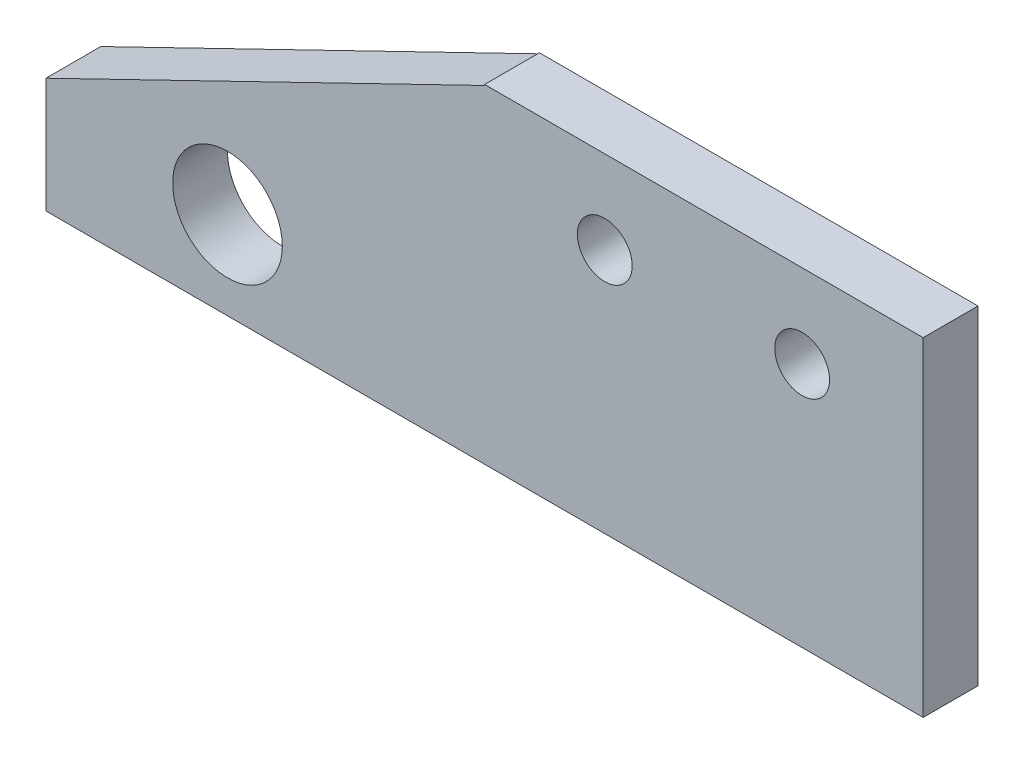
SolidWorks part; units mm, degrees
material "1060 Alloy"
ref_plane "Front Plane" through (0, 0, 0) normal (0, 0, 1) x (1, 0, 0)
ref_plane "Top Plane" through (0, 0, 0) normal (0, 1, 0) x (1, 0, 0)
ref_plane "Right Plane" through (0, 0, 0) normal (1, 0, 0) x (0, 0, -1)
sketch "Sketch4" plane through (0, 0, 0) normal (0, 0, 1) x (1, 0, 0)
  line L0 (-12.7, 4.699) -> (-5.7404, 4.699) construction
  line L1 (-12.7, 9.525) -> (12.7, 9.525)
  line L2 (-12.7, 9.525) -> (-12.7, -9.525)
  line L3 (-12.7, -9.525) -> (12.7, -9.525)
  line L4 (12.7, 9.525) -> (12.7, -9.525)
  line L5 (-12.7, 9.525) -> (12.7, -9.525) construction
  line L6 (-12.7, -9.525) -> (12.7, 9.525) construction
  line L7 (-12.7, 9.4723) -> (-38.1, 9.4723)
  line L8 (-12.7, 9.4723) -> (-12.7, -9.525)
  line L9 (-12.7, -9.525) -> (-38.1, -9.525)
  line L10 (-38.1, 9.4723) -> (-38.1, -9.525)
  line L11 (-12.7, 9.4723) -> (-38.1, -2.8622)
  circle A0 centre (-5.7404, 4.699) radius 1.5875
  circle A1 centre (-27.5896, -4.445) radius 3.175
  circle A3 centre (5.6896, 4.699) radius 1.5875
  point P0 (0, 0)
  dimension "D5" = 6.35
  dimension "D6" = 5.08
  dimension "D7" = 4.826
  dimension "D3" = 3.175
  dimension "D10" = 11.43
  dimension "D9" = 7.0104
  dimension "D1" = 19.05
  dimension "D2" = 25.4
  dimension "D4" = 25.4
  dimension "D11" = 6.6628
extrude "Boss-Extrude1" add sketch "Sketch4" along normal blind 3.175
